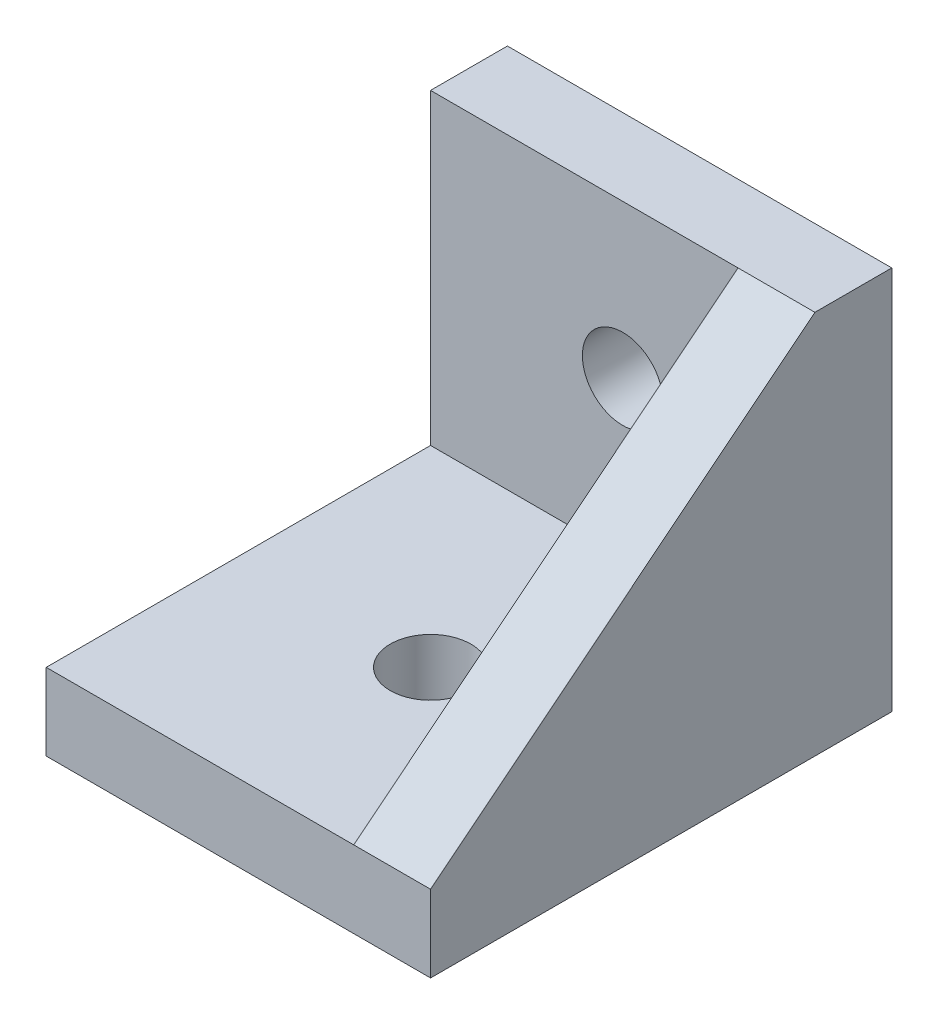
SolidWorks part; units mm, degrees
ref_plane "Top Plane" through (0, 0, 0) normal (0, 0, 1) x (1, 0, 0)
ref_plane "Front Plane" through (0, 0, 0) normal (0, 1, 0) x (1, 0, 0)
ref_plane "Right Plane" through (0, 0, 0) normal (1, 0, 0) x (0, 0, -1)
sketch "Base Profile Sketch" plane through (0, 0, 0) normal (0, 0, 1) x (1, 0, 0)
  line L1 (-6.0006, -7.5006) -> (6.0006, -7.5006)
  line L2 (-6.0006, -7.5006) -> (-6.0006, 7.5006)
  line L3 (-6.0006, 7.5006) -> (6.0006, 7.5006)
  line L4 (6.0006, -7.5006) -> (6.0006, 7.5006)
  line L5 (-6.0006, -7.5006) -> (6.0006, 7.5006) construction
  line L6 (-6.0006, 7.5006) -> (6.0006, -7.5006) construction
  point P0 (0, 0)
  dimension "D1" = 12.0012
  dimension "D2" = 15.0012
extrude "Base Profile Extrude" add sketch "Base Profile Sketch" along normal blind 3
sketch "Back Profile Sketch" plane through (0, 0, 3) normal (0, 0, 1) x (1, 0, 0)
  line L0 (-6.0006, -7.5006) -> (6.0006, -7.5006) construction
  line L1 (-6.0006, 7.5006) -> (-6.0006, -7.5006) construction
  line L2 (6.0006, -7.5006) -> (6.0006, 7.5006) construction
  line L3 (-6.0006, -7.5006) -> (6.0006, -7.5006)
  line L4 (-6.0006, -4.5006) -> (-6.0006, -7.5006)
  line L5 (6.0006, -7.5006) -> (6.0006, -4.5006)
  line L6 (-6.0006, -4.5006) -> (6.0006, -4.5006)
  dimension "D1" = 3
extrude "Back Profile Extrude" add sketch "Back Profile Sketch" along normal blind 15
sketch "Side Profile Sketch" plane through (6.0006, 0, 0) normal (1, 0, 0) x (0, 0, -1)
  line L0 (0, -7.5006) -> (0, 7.5006) construction
  line L1 (-18, -7.5006) -> (0, -7.5006) construction
  line L2 (0, -7.5006) -> (0, 7.5006)
  line L3 (-18, -7.5006) -> (0, -7.5006)
  line L4 (-18, -7.5006) -> (-18, -4.5006) construction
  line L5 (-18, -7.5006) -> (-18, -4.5006)
  line L6 (-3, 7.5006) -> (0, 7.5006) construction
  line L7 (-3, 7.5006) -> (0, 7.5006)
  line L8 (-18, -4.5006) -> (-3, 7.5006)
extrude "Side Profile Extrude" add sketch "Side Profile Sketch" along normal blind 3
sketch "Bottom Mounting Hole Sketch" plane through (0, 0, 3) normal (0, 0, 1) x (1, 0, 0)
  line L0 (-6.0006, 1.5) -> (9.0006, 1.5) construction
  line L3 (-6.0006, 7.5006) -> (-6.0006, -4.5006) construction
  line L4 (9.0006, 7.5006) -> (9.0006, -4.5006) construction
  line L5 (9.0006, 7.5006) -> (9.0006, -4.5006)
  circle A0 centre (1.5, 1.5) radius 1.575
  dimension "D1" = 3.15
extrude "Bottom Mounting Hole Cut" cut sketch "Bottom Mounting Hole Sketch" against normal up to next contours L0 A0 | A0 L0
sketch "Back Mounting Hole Sketch" plane through (0, -4.5006, 0) normal (0, 1, 0) x (1, 0, 0)
  line L0 (9.0006, -10.5) -> (-6.0006, -10.5) construction
  line L2 (-6.0006, -18) -> (-6.0006, -3) construction
  line L3 (9.0006, -3) -> (9.0006, -18) construction
  line L4 (9.0006, -3) -> (9.0006, -18)
  circle A0 centre (1.5, -10.5) radius 1.575
  dimension "D1" = 3.15
extrude "Back Mounting Hole Cut" cut sketch "Back Mounting Hole Sketch" against normal up to next contours A0
equation "\"D1@Base Profile Sketch\"=\"D2@Base Profile Sketch\"-3mm"
